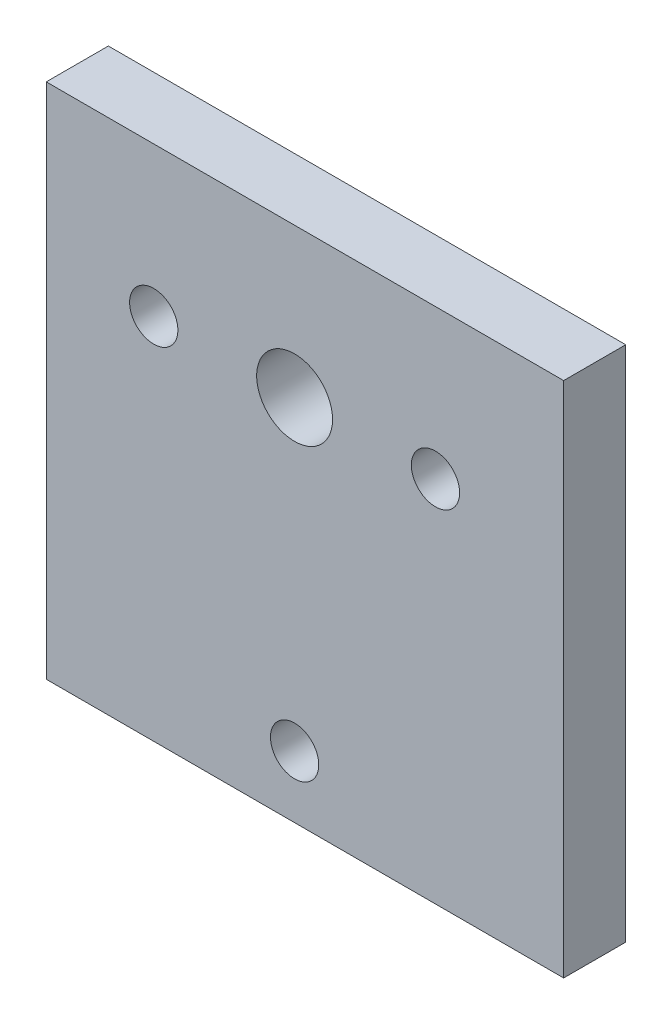
SolidWorks part; units mm, degrees
ref_plane "Front Plane" through (0, 0, 0) normal (0, 0, 1) x (1, 0, 0)
ref_plane "Top Plane" through (0, 0, 0) normal (0, 1, 0) x (1, 0, 0)
ref_plane "Right Plane" through (0, 0, 0) normal (1, 0, 0) x (0, 0, -1)
sketch "Sketch1" plane through (0, 0, 0) normal (0, 0, 1) x (1, 0, 0)
  line L0 (18.75, 18.75) -> (-18.75, 18.75)
  line L2 (-18.75, 18.75) -> (-18.75, -18.75)
  line L3 (-18.75, -18.75) -> (18.75, -18.75)
  line L4 (18.75, 18.75) -> (18.75, -18.75)
  line L5 (-18.75, 18.75) -> (18.75, -18.75) construction
  line L6 (-18.75, -18.75) -> (18.75, 18.75) construction
  circle A0 centre (-0.75, 7.9292) radius 2.75
  circle A1 centre (9.46, 7.9292) radius 1.75
  circle A2 centre (-10.96, 7.9292) radius 1.75
  circle A3 centre (-0.75, -14.25) radius 1.75
  point P0 (0, 0)
  dimension "D5" = 10.21
  dimension "D7" = 3.5
  dimension "D8" = 3.5
  dimension "D9" = 4.5
  dimension "D10" = 3.5
  dimension "D3" = 5.5
  dimension "D1" = 37.5
  dimension "D2" = 37.5
  dimension "D4" = 26.6792
  dimension "D6" = 10.21
extrude "Boss-Extrude1" add sketch "Sketch1" along normal blind 4.5
